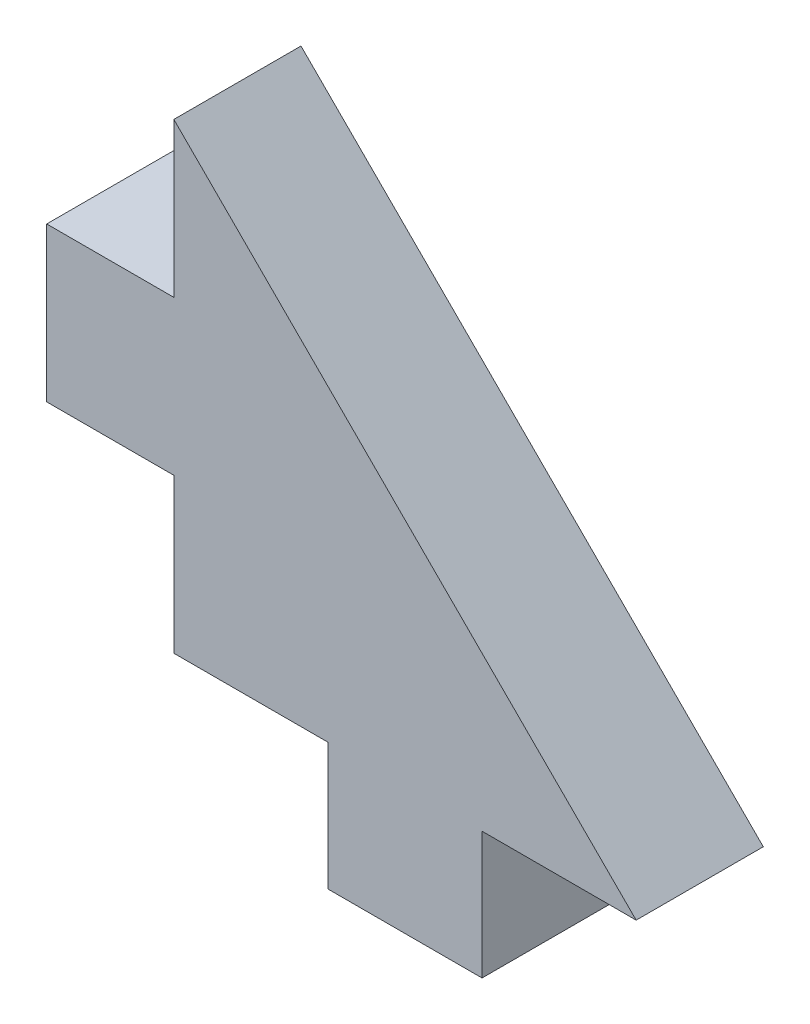
SolidWorks part; units mm, degrees
ref_plane "Front Plane" through (0, 0, 0) normal (0, 0, 1) x (1, 0, 0)
ref_plane "Top Plane" through (0, 0, 0) normal (0, 1, 0) x (1, 0, 0)
ref_plane "Right Plane" through (0, 0, 0) normal (1, 0, 0) x (0, 0, -1)
sketch "Sketch1" plane through (0, 0, 0) normal (0, 0, 1) x (1, 0, 0)
  line L0 (0, 20) -> (20, 0)
  line L1 (0, 0) -> (6.6667, 0)
  line L2 (0, 0) -> (0, 6.6667)
  line L3 (13.3333, 0) -> (20, 0)
  line L4 (0, 13.3333) -> (0, 20)
  line L5 (6.6667, 0) -> (6.6667, -5.5)
  line L6 (6.6667, -5.5) -> (13.3333, -5.5)
  line L7 (13.3333, 0) -> (13.3333, -5.5)
  line L8 (0, 13.3333) -> (-5.5, 13.3333)
  line L10 (0, 6.6667) -> (-5.5, 6.6667)
  line L11 (-5.5, 13.3333) -> (-5.5, 6.6667)
  dimension "D1" = 20
  dimension "D2" = 20
  dimension "D3" = 5.5
extrude "Boss-Extrude1" add sketch "Sketch1" along normal blind 5.5
equation "\"mat\"=\"mat@hobby motor air spinner.assembly\""
equation "\"D3@Sketch1\" = \"mat\""
equation "\"D1@Boss-Extrude1\" = \"mat\""
